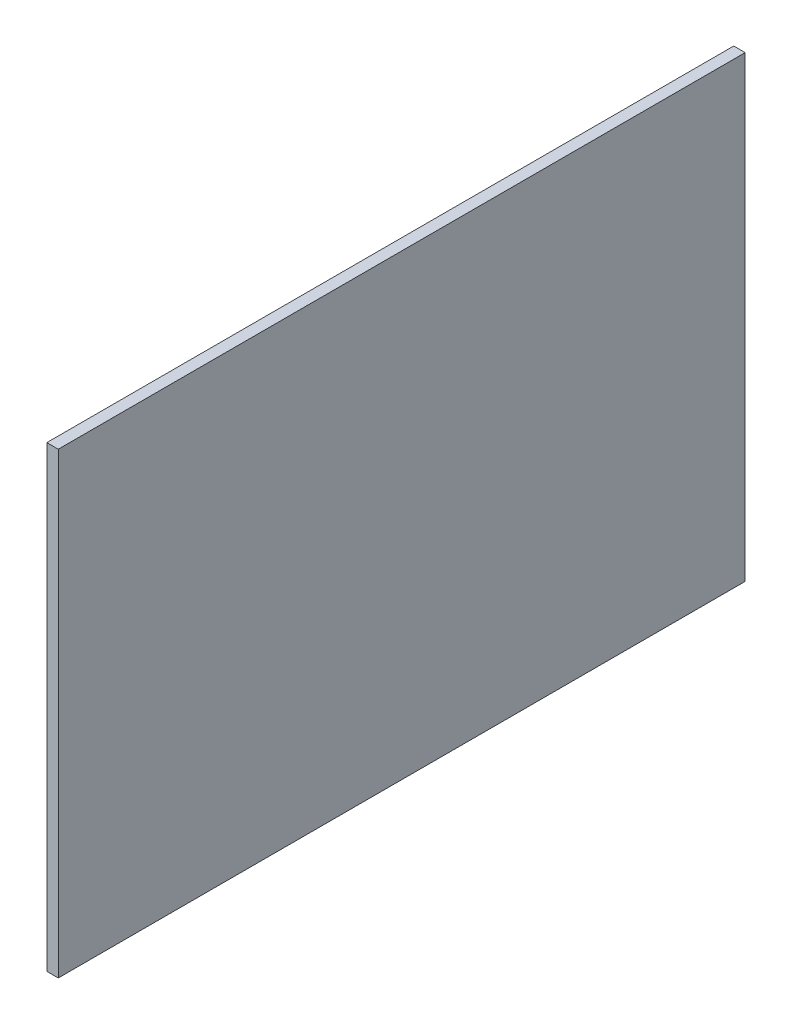
SolidWorks part; units mm, degrees
ref_plane "Front Plane" through (0, 0, 0) normal (0, 0, 1) x (1, 0, 0)
ref_plane "Top Plane" through (0, 0, 0) normal (0, 1, 0) x (1, 0, 0)
ref_plane "Right Plane" through (0, 0, 0) normal (1, 0, 0) x (0, 0, -1)
sketch "Sketch1" plane through (-5292.4306, 3271.8532, 87.3435) normal (1, 0, 0) x (0, 0, -1)
  line L4 (-1568.3462, 78.7188) -> (-968.3462, 78.7188)
  line L5 (-1568.3462, 478.7188) -> (-1568.3462, 78.7188)
  line L6 (-968.3462, 478.7188) -> (-1568.3462, 478.7188)
  line L7 (-968.3462, 478.7188) -> (-968.3462, 78.7188)
  point P0 (-968.3462, 78.7188)
  point P1 (-1633.2032, 78.7188)
  point P4 (-970.5526, 78.7188)
  point P8 (-963.3648, 538.7188)
  dimension "D1" = 400
  dimension "D2" = 600
extrude "Boss-Extrude1" add sketch "Sketch1" along normal blind 10
